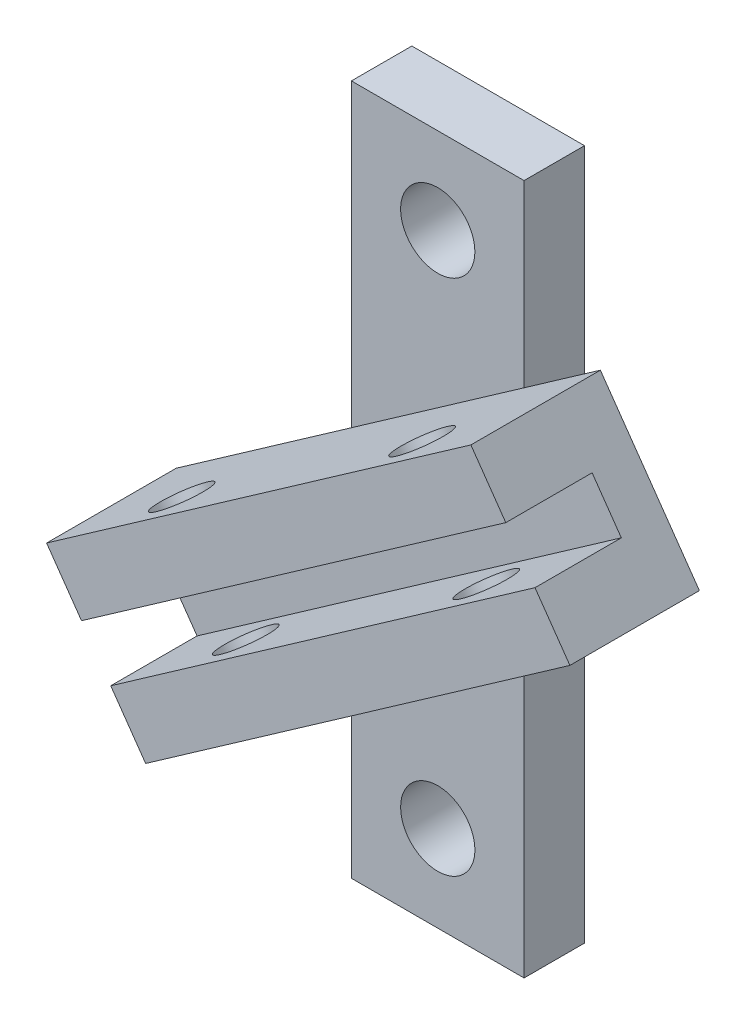
SolidWorks part; units mm, degrees
ref_plane "Ebene vorne" through (0, 0, 0) normal (0, 0, 1) x (1, 0, 0)
ref_plane "Ebene oben" through (0, 0, 0) normal (0, 1, 0) x (1, 0, 0)
ref_plane "Ebene rechts" through (0, 0, 0) normal (1, 0, 0) x (0, 0, -1)
sketch "Skizze1" plane through (0, 0, 0) normal (0, 0, 1) x (1, 0, 0)
  line L0 (10, 80) -> (10, 0) construction
  line L1 (0, 0) -> (20, 0)
  line L2 (0, 0) -> (0, 80)
  line L3 (0, 80) -> (20, 80)
  line L4 (20, 0) -> (20, 80)
  line L5 (0, 70) -> (20, 70) construction
  line L6 (0, 40) -> (20, 40) construction
  circle A0 centre (10, 70) radius 4.3
  circle A1 centre (10, 10) radius 4.3
  dimension "D4" = 8.6
  dimension "D1" = 80
  dimension "D2" = 20
  dimension "D3" = 10
extrude "Aufsatz-Linear austragen1" add sketch "Skizze1" along normal blind 7
sketch "Skizze2" plane through (0, 0, 7) normal (0, 0, 1) x (1, 0, 0)
  line L0 (-20.3103, 30.9842) -> (-8.8388, 14.6012)
  line L1 (-8.8388, 14.6012) -> (40.3103, 49.0158)
  line L2 (40.3103, 49.0158) -> (28.8388, 65.3988)
  line L3 (28.8388, 65.3988) -> (-20.3103, 30.9842)
  line L4 (0, 80) -> (20, 80)
  line L5 (4.2642, 48.1915) -> (15.7358, 31.8085) construction
  line L6 (0, 0) -> (20, 0)
  line L7 (10, 0) -> (10, 80) construction
  line L8 (-16.2666, 25.2092) -> (32.8825, 59.6238)
  line L9 (-12.8825, 20.3762) -> (36.2666, 54.7908)
  line L10 (-14.5746, 22.7927) -> (34.5746, 57.2073) construction
  point P17 (10, 40)
  line M6 (0, 80) -> (0, 0)
  line M8 (20, 0) -> (20, 80)
  dimension "D1" = 20
  dimension "D2" = 60
  dimension "D3" = 35
  dimension "D4" = 5.9
  dimension "D5" = 40
extrude "Aufsatz-Linear austragen2" add sketch "Skizze2" along normal blind 15 contours L9 L1 L2 M8 | L9 L2 L8 M8 | L8 L2 L3 M8 | L8 L3 M6 M8 | L9 L8 M6 M8 | L9 L1 M6 M8 | L9 L0 L1 M6 | L0 L9 L8 M6 | L0 L8 L3 M6
sketch "Skizze3" plane through (0, 0, 22) normal (0, 0, 1) x (1, 0, 0)
  line L0 (-12.8825, 20.3762) -> (36.2666, 54.7908)
  line L1 (36.2666, 54.7908) -> (32.8825, 59.6238)
  line L2 (32.8825, 59.6238) -> (-16.2666, 25.2092)
  line L4 (-16.2666, 25.2092) -> (-12.8825, 20.3762)
extrude "Schnitt-Linear austragen1" cut sketch "Skizze3" against normal blind 10
sketch "Skizze5" plane through (-21.2397, 30.3335, 0) normal (-0.5736, 0.8192, 0) x (0.8192, 0.5736, 0)
  line L0 (1.1346, -17) -> (61.1346, -17) construction
  line L1 (1.1346, -7) -> (61.1346, -7)
  line L2 (1.1346, -7) -> (1.1346, -22)
  line L3 (1.1346, -22) -> (61.1346, -22)
  line L4 (61.1346, -7) -> (61.1346, -22)
  line L5 (48.1346, -7) -> (48.1346, -22) construction
  line L6 (31.1346, -7) -> (31.1346, -22) construction
  circle A0 centre (48.1346, -17) radius 3
  circle A1 centre (14.1346, -17) radius 3
  dimension "D1" = 6
  dimension "D2" = 13
  dimension "D3" = 5
hole_wizard "Ø6.0 (6) Durchmesser Bohrung1" positions "Skizze6" profile "Skizze7" hole size "Ø6.0" standard "DIN" end condition through all
sketch "Skizze6" plane through (-21.2397, 30.3335, 0) normal (-0.5736, 0.8192, 0) x (0.8192, 0.5736, 0)
  point P0 (48.1346, -17)
  point P3 (14.1346, -17)
sketch "Skizze7" plane through (18.1898, 57.9423, 17) normal (0, 0, 1) x (-0.8192, -0.5736, 0)
  line L0 (0, 0) -> (0, 60.1514)
  line L1 (0, 60.1514) -> (3, 60.1514)
  line L2 (3, 60.1514) -> (3, 0)
  line L5 (3, 0) -> (0, 0)
  line L11 (0, -6.35) -> (0, 107.95) construction
  dimension "Bohrerdurchmesser" = 6
  dimension "Bohrungstiefe" = 60.1514
